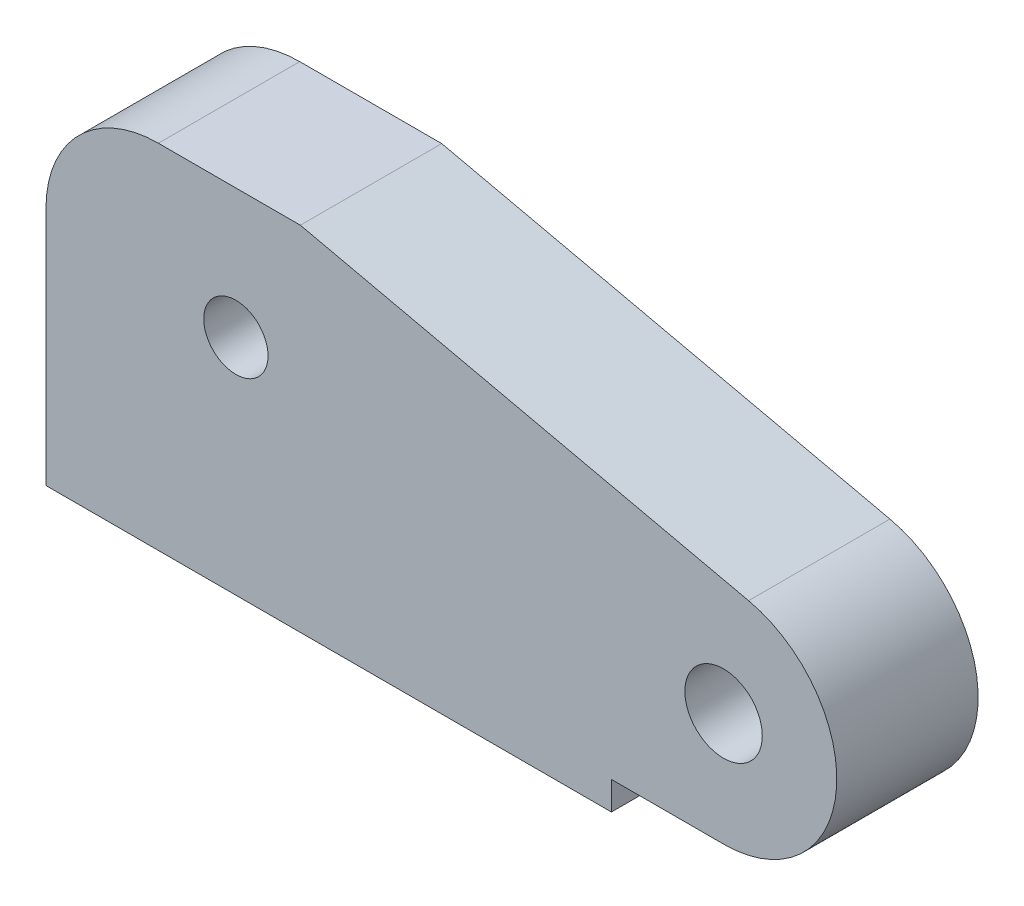
SolidWorks part; units mm, degrees
ref_plane "Alzado" through (0, 0, 0) normal (0, 0, 1) x (1, 0, 0)
ref_plane "Planta" through (0, 0, 0) normal (0, 1, 0) x (1, 0, 0)
ref_plane "Vista lateral" through (0, 0, 0) normal (1, 0, 0) x (0, 0, -1)
sketch "Croquis1" plane through (0, 0, 0) normal (0, 0, 1) x (1, 0, 0)
  line L0 (-58.5, -33.5) -> (-58.5, -16.5)
  line L1 (-50.5498, -8.5498) -> (-40.5056, -8.5498)
  line L2 (-40.5056, -8.5498) -> (-8.7957, -15.6986)
  line L3 (-10.567, -31.5) -> (-18.5, -31.5)
  line L4 (-18.5, -31.5) -> (-18.5, -33.5)
  line L5 (-18.5, -33.5) -> (-58.5, -33.5)
  circle A0 centre (-45.067, -17.7) radius 2.2736
  circle A1 centre (-10.567, -23.5) radius 2.7394
  arc A3 (-8.7957, -15.6986) -> (-10.567, -31.5) centre (-10.5547, -23.5014) cw
  arc A4 (-58.5, -16.5) -> (-50.5498, -8.5498) centre (-50.5498, -16.5) cw
extrude "Saliente-Extruir1" add sketch "Croquis1" along normal blind 10
